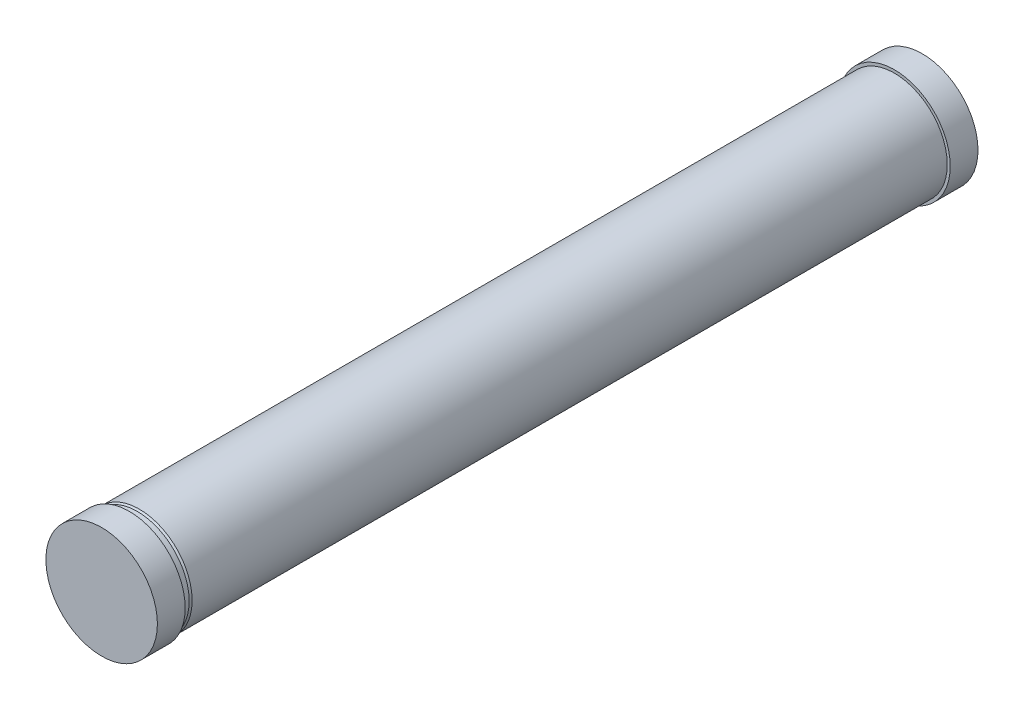
SolidWorks part; units mm, degrees
ref_plane "Front Plane" through (0, 0, 0) normal (0, 0, 1) x (1, 0, 0)
ref_plane "Top Plane" through (0, 0, 0) normal (0, 1, 0) x (1, 0, 0)
ref_plane "Right Plane" through (0, 0, 0) normal (1, 0, 0) x (0, 0, -1)
sketch "Sketch1" plane through (0, 0, 0) normal (1, 0, 0) x (0, 0, -1)
  line L0 (296.619, 1.7288) -> (1519.9523, 1.7288) construction
  line L1 (531.9431, 0) -> (1658.8798, 0) construction
  line L2 (386.8719, 0) -> (386.8719, 112.8517) construction
  line L3 (386.8719, -112.8517) -> (386.8719, 0) construction
  line L4 (1668.9392, 70.4031) -> (1723.8999, 183.2068) construction
  line L5 (531.9431, 0) -> (531.9431, 73.5269) construction
  line L6 (531.9431, 73.5269) -> (572.6476, 73.5269)
  line L7 (572.6476, 73.5269) -> (577.0918, 67.2792)
  line L8 (577.0918, 67.2792) -> (588.1132, 67.2792)
  line L9 (588.1132, 67.2792) -> (591.701, 69.8314)
  line L10 (591.701, 69.8314) -> (1619.651, 67.2792)
  line L11 (1619.651, 67.2792) -> (1619.651, 70.4031)
  line L12 (1619.651, 70.4031) -> (1658.8798, 70.4031)
  line L13 (1658.8798, 70.4031) -> (1658.8798, 0)
  line L14 (1668.9392, 70.4031) -> (1668.9392, 197.5811) construction
  line L15 (1095.4114, 0) -> (1095.4114, 68.5808) construction
  line L16 (2810.9399, 142.3756) -> (2810.9399, 0)
  line L17 (645.5356, 136.0583) -> (652.7912, 141.2195)
  line L18 (531.9431, 0) -> (2810.9399, 0) construction
  line L19 (2731.6077, 142.3756) -> (2810.9399, 142.3756)
  line L20 (1671.4415, 0) -> (1671.4415, 138.6905) construction
  line L21 (614.2596, 148.6929) -> (623.247, 136.0583)
  line L22 (623.247, 136.0583) -> (645.5356, 136.0583)
  line L23 (652.7912, 141.2195) -> (2731.6077, 136.0583)
  line L24 (531.9431, 148.6929) -> (614.2596, 148.6929)
  line L25 (2731.6077, 136.0583) -> (2731.6077, 142.3756)
  line L26 (531.9431, 0) -> (531.9431, 148.6929) construction
sketch "Sketch2" plane through (0, 0, 0) normal (1, 0, 0) x (0, 0, -1)
  line L0 (0, 130.4898) -> (0, -10.0102)
  line L1 (0, -10.0102) -> (2068, -10.0102)
  line L15 (2068, 130.4898) -> (2068, -10.0102)
  line L16 (90, 120.4898) -> (95, 122.9898)
  line L17 (0, -10.0102) -> (2068, -10.0102) construction
  line L18 (1998, 130.4898) -> (2068, 130.4898)
  line L20 (70, 130.4898) -> (75, 120.4898)
  line L21 (75, 120.4898) -> (90, 120.4898)
  line L22 (95, 122.9898) -> (1998, 122.9898)
  line L23 (0, 130.4898) -> (70, 130.4898)
  line L24 (1998, 122.9898) -> (1998, 130.4898)
  dimension "D1" = 2068
  dimension "D2" = 70
  dimension "D3" = 15
  dimension "D4" = 10
  dimension "D5" = 5
  dimension "D6" = 133
  dimension "D7" = 5
  dimension "D8" = 140.5
  dimension "D9" = 70
revolve "Revolve1" add sketch "Sketch2" angle 360 about L17
